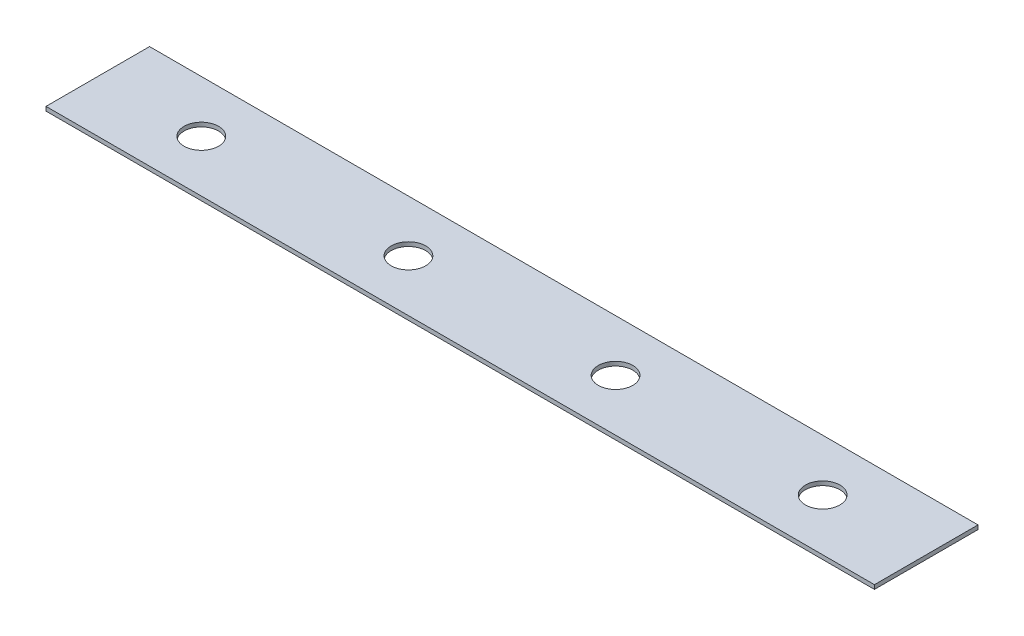
SolidWorks part; units mm, degrees
material "Plain Carbon Steel"
ref_plane "Front Plane" through (0, 0, 0) normal (0, 0, 1) x (1, 0, 0)
ref_plane "Top Plane" through (0, 0, 0) normal (0, 1, 0) x (1, 0, 0)
ref_plane "Right Plane" through (0, 0, 0) normal (1, 0, 0) x (0, 0, -1)
sketch "Sketch1" plane through (0, 0, 0) normal (1, 0, 0) x (0, 0, -1)
  line L1 (0, 0) -> (38.1, 0)
  line L2 (0, 0) -> (0, 1.5189)
  line L3 (0, 1.5189) -> (38.1, 1.5189)
  line L4 (38.1, 0) -> (38.1, 1.5189)
  dimension "D1" = 38.1
  dimension "D2" = 1.5189
extrude "Boss-Extrude1" add sketch "Sketch1" along normal blind 304.8
sketch "Sketch2" plane through (0, 0, 0) normal (0, 0, 1) x (1, 0, 0)
  line L0 (0, 0) -> (304.8, 0) construction
  point P4 (152.4, 0)
sketch "Sketch3" plane through (0, 1.5189, 0) normal (0, 1, 0) x (1, 0, 0)
  line L0 (114.3, 19.05) -> (38.1, 19.05) construction
  line L2 (114.3, 19.05) -> (190.5, 19.05) construction
  line L3 (190.5, 19.05) -> (266.7, 19.05) construction
  line L4 (266.7, 19.05) -> (304.8, 19.05) construction
  line L5 (304.8, 38.1) -> (304.8, 0) construction
  line L6 (38.1, 19.05) -> (0, 19.05) construction
  line L7 (0, 38.1) -> (0, 0) construction
  circle A0 centre (114.3, 19.05) radius 6.35
  circle A1 centre (190.5, 19.05) radius 6.35
  circle A2 centre (266.7, 19.05) radius 6.35
  circle A3 centre (38.1, 19.05) radius 6.35
  dimension "D1" = 12.7
  dimension "D2" = 12.7
  dimension "D3" = 12.7
  dimension "D4" = 12.7
  dimension "D5" = 38.1
extrude "Cut-Extrude1" cut sketch "Sketch3" against normal through all
